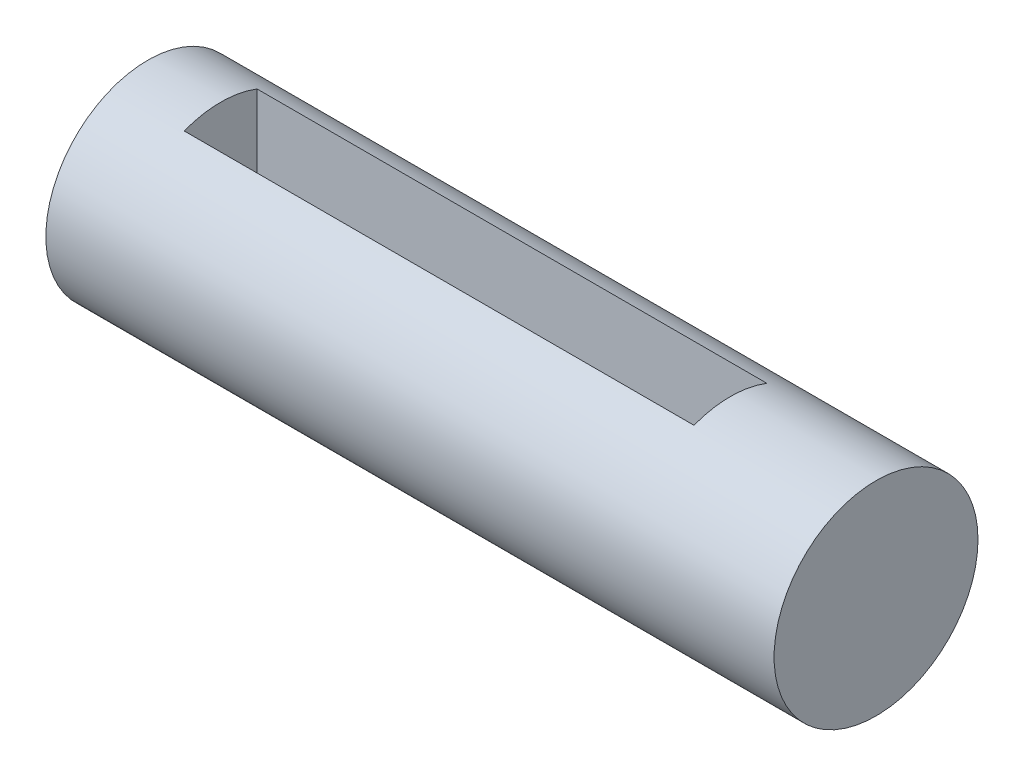
SolidWorks part; units mm, degrees
ref_plane "Front Plane" through (0, 0, 0) normal (0, 0, 1) x (1, 0, 0)
ref_plane "Top Plane" through (0, 0, 0) normal (0, 1, 0) x (1, 0, 0)
ref_plane "Right Plane" through (0, 0, 0) normal (1, 0, 0) x (0, 0, -1)
sketch "Sketch1" plane through (0, 0, 0) normal (1, 0, 0) x (0, 0, -1)
  circle A0 centre (0, 0) radius 7
  dimension "D1" = 14
extrude "Boss-Extrude1" add sketch "Sketch1" along normal blind 50
sketch "Sketch2" plane through (0, 0, 0) normal (0, 0, 1) x (1, 0, 0)
  line L0 (50, 7) -> (0, 7) construction
  line L1 (5, 7) -> (40, 7)
  line L2 (5, 7) -> (5, -7)
  line L3 (5, -7) -> (40, -7)
  line L4 (40, 7) -> (40, -7)
  line L5 (0, -7) -> (50, -7) construction
  line L6 (0, 7) -> (0, -7) construction
  line L7 (50, -7) -> (50, 7) construction
  dimension "D1" = 5
  dimension "D2" = 10
extrude "Cut-Extrude1" cut sketch "Sketch2" against normal mid plane 5
sketch "Sketch3" plane through (40, 0, 0) normal (-1, 0, 0) x (0, 0, 1)
  point P0 (0, 0)
sketch "Sketch4" plane through (5, 0, 0) normal (1, 0, 0) x (0, 0, -1)
  point P0 (0, 0)
